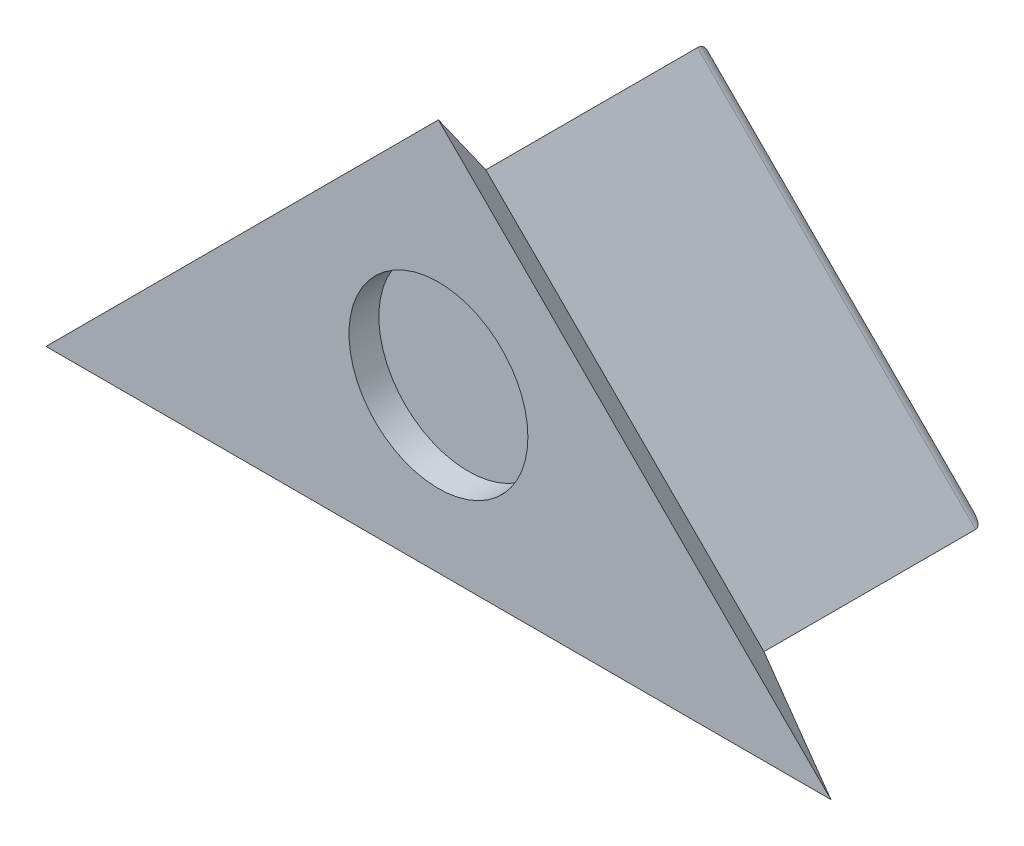
SolidWorks part; units mm, degrees
ref_plane "Front Plane" through (0, 0, 0) normal (0, 0, 1) x (1, 0, 0)
ref_plane "Top Plane" through (0, 0, 0) normal (0, 1, 0) x (1, 0, 0)
ref_plane "Right Plane" through (0, 0, 0) normal (1, 0, 0) x (0, 0, -1)
sketch "Sketch1" plane through (0, 0, 0) normal (0, 0, 1) x (1, 0, 0)
  line L0 (9.3327, -89.9716) -> (0, -80.6389)
  line L1 (0, -80.6389) -> (-9.3327, -89.9716)
  line L2 (-9.3327, -89.9716) -> (9.3327, -89.9716)
  line L3 (-14.2369, -94.5166) -> (-24.1829, -104.4625)
  line L4 (-14.2369, -114.4084) -> (-14.2369, -94.5166)
  line L5 (-24.1829, -104.4625) -> (-14.2369, -114.4084)
  line L6 (-14.2369, -94.5166) -> (-24.1829, -104.4625) construction
  line L7 (-14.2369, -114.4084) -> (-14.2369, -94.5166) construction
  line L8 (-24.1829, -104.4625) -> (-14.2369, -114.4084) construction
  line L9 (14.2369, -114.4084) -> (24.1829, -104.4625)
  line L10 (14.2369, -94.5166) -> (14.2369, -114.4084)
  line L11 (24.1829, -104.4625) -> (14.2369, -94.5166)
  line L12 (14.2369, -114.4084) -> (24.1829, -104.4625) construction
  line L13 (14.2369, -94.5166) -> (14.2369, -114.4084) construction
  line L14 (24.1829, -104.4625) -> (14.2369, -94.5166) construction
  line L15 (9.9459, -90.2256) -> (0, -80.2796)
  line L16 (-9.9459, -90.2256) -> (9.9459, -90.2256)
  line L17 (0, -80.2796) -> (-9.9459, -90.2256)
  line L18 (9.9459, -90.2256) -> (0, -80.2796) construction
  line L19 (-9.9459, -90.2256) -> (9.9459, -90.2256) construction
  line L20 (0, -80.2796) -> (-9.9459, -90.2256) construction
  line L22 (66.56, -99.8625) -> (55.36, -99.8625)
  line L23 (66.56, -109.0625) -> (66.56, -99.8625)
  line L24 (55.36, -109.0625) -> (66.56, -109.0625)
  line L25 (55.36, -99.8625) -> (55.36, -109.0625)
  line L26 (66.56, -99.8625) -> (55.36, -99.8625) construction
  line L27 (66.56, -109.0625) -> (66.56, -99.8625) construction
  line L28 (55.36, -109.0625) -> (66.56, -109.0625) construction
  line L29 (55.36, -99.8625) -> (55.36, -109.0625) construction
  dimension "D1" = 0
  dimension "D2" = 0
  dimension "D3" = 0
  dimension "D4" = 0
  dimension "D5" = 0.254
extrude "Boss-Extrude1" add sketch "Sketch1" against normal blind 7.5
ref_plane "Plane4" through (0, 0, 1.5875) normal (0, 0, 1) x (1, 0, 0)
sketch "Sketch2" plane through (0, 0, 1.5875) normal (0, 0, 1) x (1, 0, 0)
  line L0 (-13.1653, -91.5591) -> (13.1653, -91.5591)
  line L1 (13.1653, -91.5591) -> (0, -78.3938)
  line L2 (0, -78.3938) -> (-13.1653, -91.5591)
  line L3 (-9.3327, -89.9716) -> (9.3327, -89.9716)
  line L4 (9.3327, -89.9716) -> (0, -80.6389)
  line L5 (0, -80.6389) -> (-9.3327, -89.9716)
  line L6 (-9.3327, -89.9716) -> (9.3327, -89.9716) construction
  line L7 (9.3327, -89.9716) -> (0, -80.6389) construction
  line L8 (0, -80.6389) -> (-9.3327, -89.9716) construction
  dimension "D1" = 0
  dimension "D2" = 1.5875
loft "Loft1" add profiles "Sketch2" section face at (0, -86.8607, 0) section "Sketch2"
fillet "Fillet1" radius 0.4 3 edges at (4.6664, -85.3052, -7.5) (-4.6664, -85.3052, -7.5) (0, -89.9716, -7.5)
sketch "Sketch3" plane through (0, 0, 1.5875) normal (0, 0, 1) x (1, 0, 0)
  line L0 (0, -89.9716) -> (0, -89.1058) construction
  line L1 (-9.3327, -89.9716) -> (9.3327, -89.9716) construction
  line L2 (2.1213, -83.9845) -> (2.7335, -83.3724) construction
  line L3 (9.3327, -89.9716) -> (0, -80.6389) construction
  line L4 (2.1213, -83.9845) -> (0.7893, -82.6525) construction
  circle A0 centre (0, -86.1058) radius 3
  point P10 (0, 0)
  point P12 (0, 0)
  point P13 (0, 0)
  point P15 (0, 0)
  point P16 (0, 0)
  point P17 (0, 0)
  point P18 (0, 0)
  point P19 (0, -86.1058)
  dimension "D1" = 6
extrude "Cut-Extrude2" cut sketch "Sketch3" against normal blind 1
